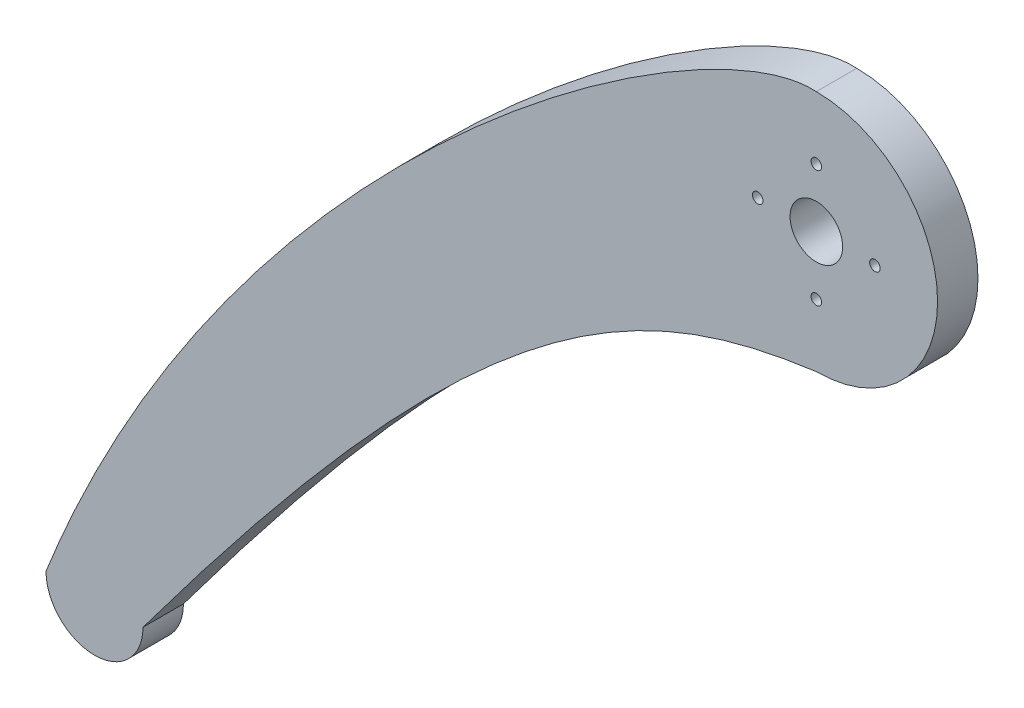
SolidWorks part; units mm, degrees
ref_plane "Front Plane" through (0, 0, 0) normal (0, 0, 1) x (1, 0, 0)
ref_plane "Top Plane" through (0, 0, 0) normal (0, 1, 0) x (1, 0, 0)
ref_plane "Right Plane" through (0, 0, 0) normal (1, 0, 0) x (0, 0, -1)
sketch "Sketch1" plane through (0, 0, 0) normal (0, 0, 1) x (1, 0, 0)
  line L0 (0, 15) -> (-14.2306, 15.974) construction
  line L1 (-14.2306, 15.974) -> (-71.5426, -23.8967) construction
  line L2 (-71.5426, -23.8967) -> (-95.2936, -84.0243) construction
  line L3 (0, -15) -> (-22.042, -17.9795) construction
  line L4 (-22.042, -17.9795) -> (-40.9384, -27.1904) construction
  line L5 (-40.9384, -27.1904) -> (-83.2936, -84.0243) construction
  arc A0 (0, -15) -> (0, 15) centre (0, 0) ccw
  arc A2 (-95.2936, -84.0243) -> (-83.2936, -84.0243) centre (-89.2936, -84.0243) ccw
  spline S0 degree 3 poles (0, 15) (-14.2306, 15.974) (-71.5426, -23.8967) (-95.2936, -84.0243) knots 0 0 0 0 1 1 1 1
  spline S1 degree 3 poles (0, -15) (-22.042, -17.9795) (-40.9384, -27.1904) (-83.2936, -84.0243) knots 0 0 0 0 1 1 1 1
  dimension "D1" = 30
  dimension "D2" = 12
extrude "Boss-Extrude1" add sketch "Sketch1" along normal blind 5
sketch "Sketch2" plane through (0, 0, 5) normal (0, 0, 1) x (1, 0, 0)
  circle A0 centre (0, 0) radius 3.25
  circle A1 centre (0, 7.25) radius 0.65
  circle A2 centre (-7.25, 0) radius 0.65
  circle A3 centre (0, -7.25) radius 0.65
  circle A4 centre (7.25, 0) radius 0.65
  dimension "D1" = 6.5
  dimension "D6" = 1.3
  dimension "D7" = 1.3
  dimension "D8" = 1.3
  dimension "D9" = 1.3
  dimension "D2" = 7.25
  dimension "D3" = 7.25
  dimension "D4" = 7.25
  dimension "D5" = 7.25
extrude "Cut-Extrude1" cut sketch "Sketch2" against normal blind 5
